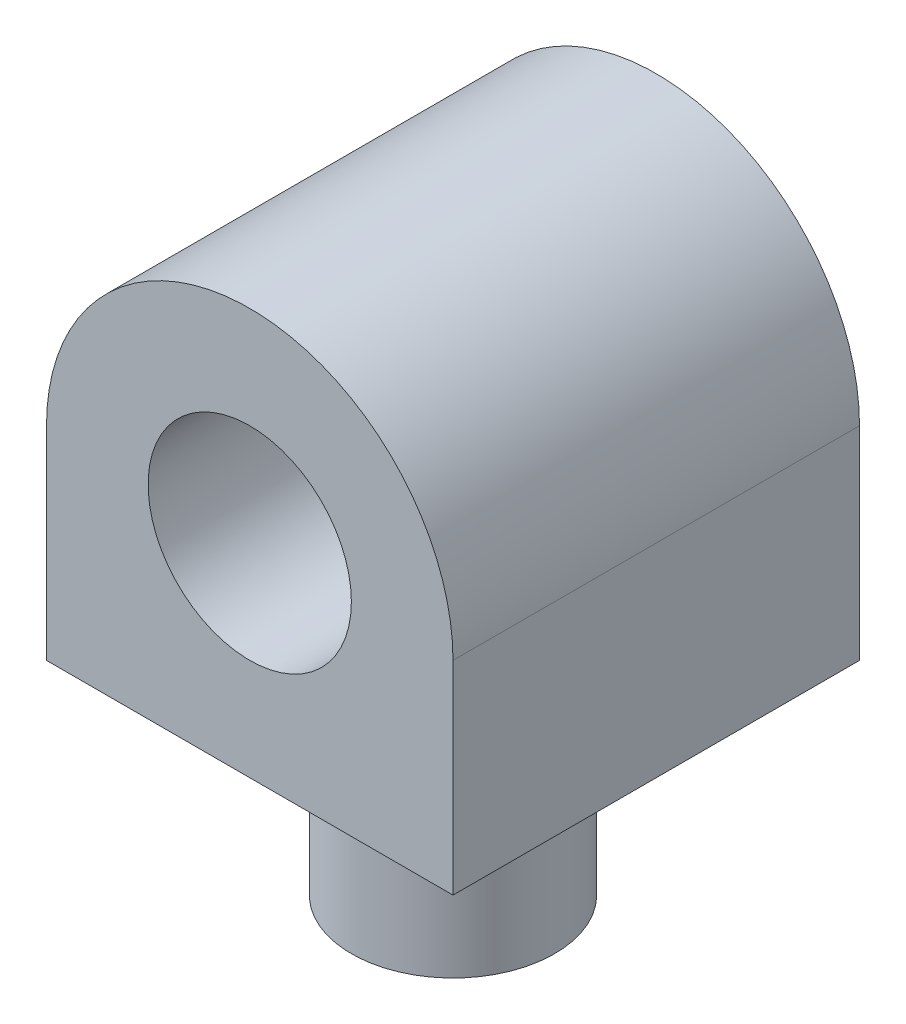
SolidWorks part; units mm, degrees
ref_plane "Front Plane" through (0, 0, 0) normal (0, 0, 1) x (1, 0, 0)
ref_plane "Top Plane" through (0, 0, 0) normal (0, 1, 0) x (1, 0, 0)
ref_plane "Right Plane" through (0, 0, 0) normal (1, 0, 0) x (0, 0, -1)
sketch "sketch1_link5" plane through (0, 0, 0) normal (0, 0, 1) x (1, 0, 0)
  line L0 (-30, 0) -> (-30, -30)
  line L1 (30, 0) -> (30, -30)
  line L2 (-30, -30) -> (30, -30)
  circle A0 centre (0, 0) radius 15
  arc A1 (-30, 0) -> (30, 0) centre (0, 0) cw
  point P5 (0, 30)
  point P8 (0, -30)
  dimension "D1" = 30
  dimension "D2" = 30
  dimension "D3" = 60
extrude "Boss-Extrude1" add sketch "sketch1_link5" along normal mid plane 60
sketch "sketch2_link5" plane through (0, -30, 0) normal (0, -1, 0) x (1, 0, 0)
  circle A0 centre (0, 0) radius 15
  dimension "D1" = 30
extrude "Boss-Extrude2" add sketch "sketch2_link5" along normal blind 30
